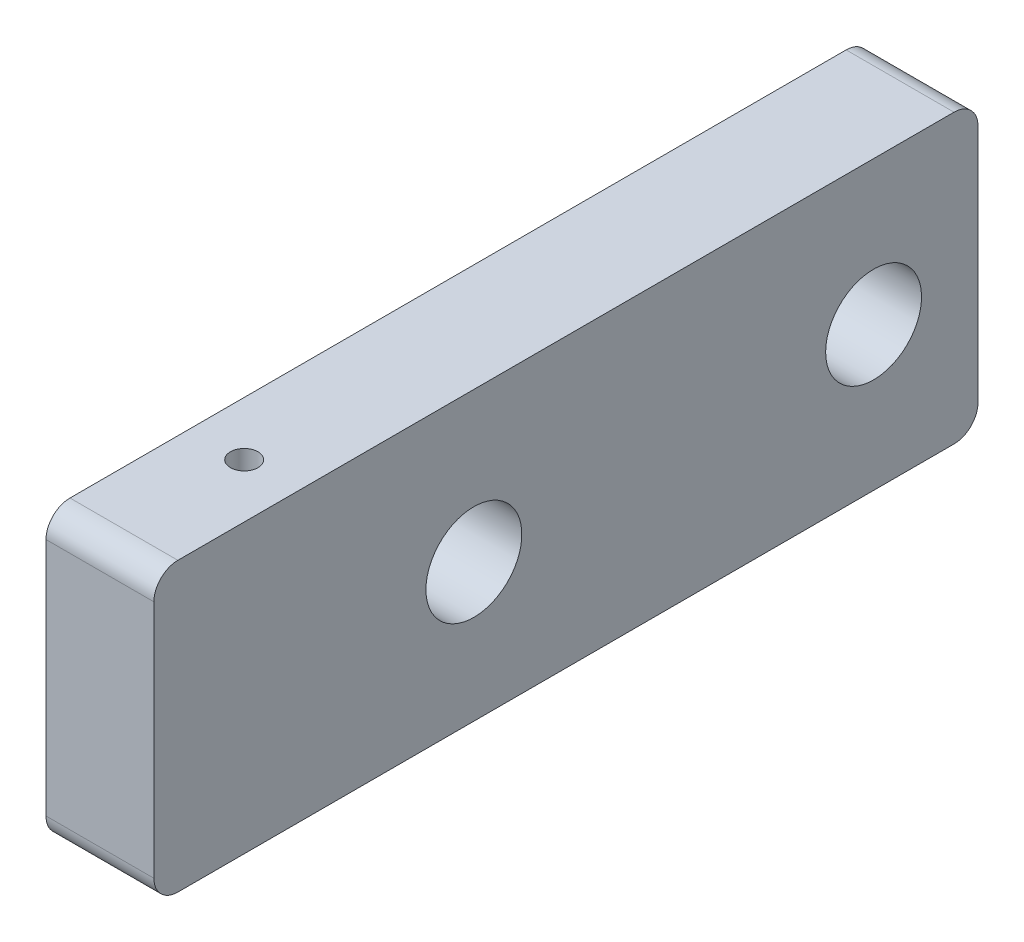
SolidWorks part; units mm, degrees
ref_plane "Front Plane" through (0, 0, 0) normal (0, 0, 1) x (1, 0, 0)
ref_plane "Top Plane" through (0, 0, 0) normal (0, 1, 0) x (1, 0, 0)
ref_plane "Right Plane" through (0, 0, 0) normal (1, 0, 0) x (0, 0, -1)
ref_plane "Plane1" through (74.9692, 0, 0) normal (-1, 0, 0) x (0, 0, 1)
sketch "Sketch1" plane through (74.9692, 0, 0) normal (-1, 0, 0) x (0, 0, 1)
  line L0 (54.6932, 19.7712) -> (54.6932, -4.2)
  line L1 (54.6932, -4.2) -> (-14.0548, -4.2)
  line L3 (54.6932, 19.7712) -> (-14.0548, 19.7712)
  line L4 (-14.0548, -4.2) -> (-14.0548, 19.7712)
  line L5 (54.6932, -0.6158) -> (-14.0548, 19.7712) construction
  line L6 (54.6932, 14.5993) -> (-14.0548, -4.2) construction
  point P0 (28, 7.3)
extrude "Boss-Extrude1" add sketch "Sketch1" along normal blind 9
sketch "Sketch2" plane through (65.9692, 0, 0) normal (-1, 0, 0) x (0, 0, 1)
  circle A0 centre (28, 7.3) radius 4
  dimension "D1" = 8
extrude "Cut-Extrude1" cut sketch "Sketch2" against normal blind 9
fillet "Fillet1" radius 2 4 edges at (70.4692, -4.2, -14.0548) (70.4692, 19.7712, 54.6932) (70.4692, -4.2, 54.6932) (70.4692, 19.7712, -14.0548)
sketch "Sketch3" plane through (0, 19.7712, 0) normal (0, 1, 0) x (1, 0, 0)
  circle A0 centre (70.4692, -42.6593) radius 1.15
  dimension "D1" = 2.3
extrude "Cut-Extrude2" cut sketch "Sketch3" against normal blind 5
sketch "Sketch4" plane through (65.9692, 0, 0) normal (-1, 0, 0) x (0, 0, 1)
  circle A0 centre (-5.3448, 7.7856) radius 4
  dimension "D1" = 8
extrude "Cut-Extrude3" cut sketch "Sketch4" against normal up to next
